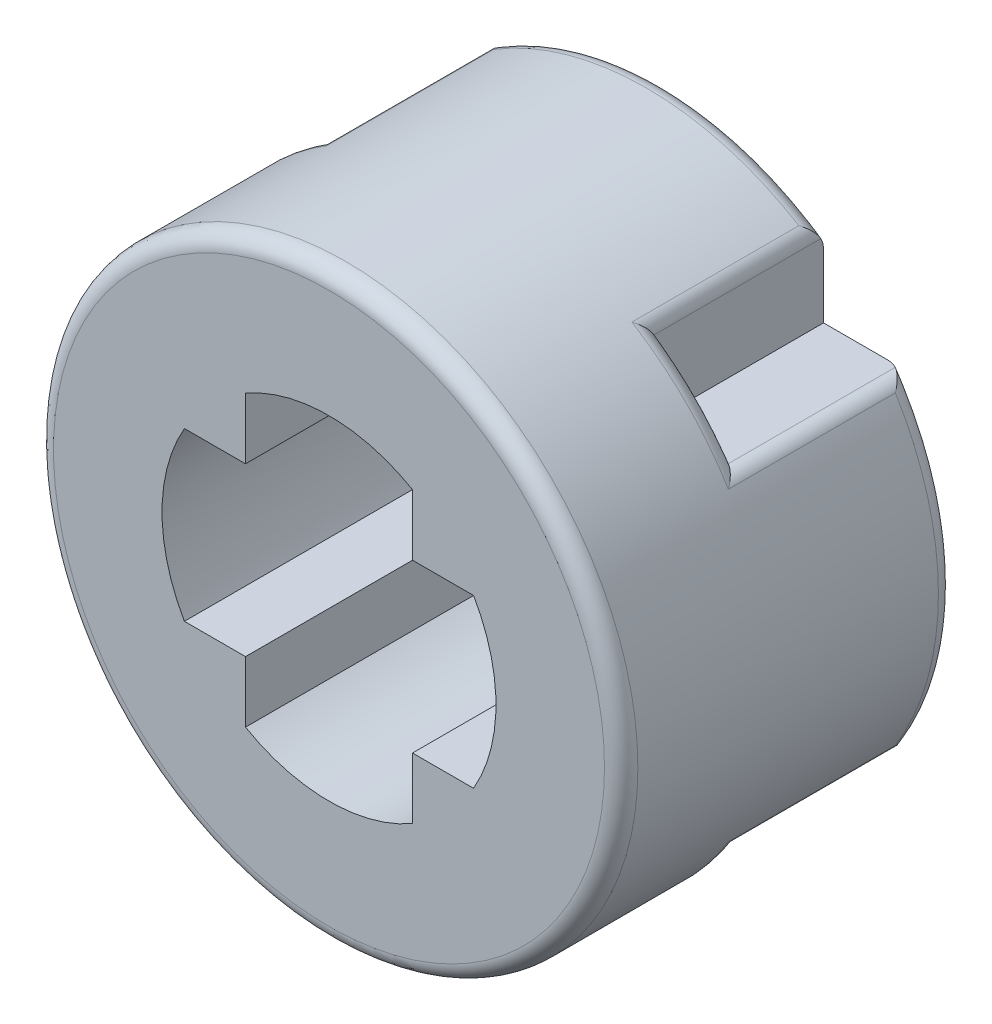
SolidWorks part; units mm, degrees
material "PBT General Purpose"
ref_plane "Front Plane" through (0, 0, 0) normal (0, 0, 1) x (1, 0, 0)
ref_plane "Top Plane" through (0, 0, 0) normal (0, 1, 0) x (1, 0, 0)
ref_plane "Right Plane" through (0, 0, 0) normal (1, 0, 0) x (0, 0, -1)
sketch "Sketch1" plane through (0, 0, 0) normal (0, 0, 1) x (1, 0, 0)
  line L0 (1, -1) -> (1.7321, -1)
  line L2 (-1, -1.7321) -> (-1, -1)
  line L4 (1, -1.7321) -> (1, -1)
  line L7 (-1.7321, -1) -> (-1, -1)
  line L9 (-1.7321, 1) -> (-1, 1)
  line L13 (1, 1) -> (1, 1.7321)
  line L14 (1, 1) -> (1.7321, 1)
  line L15 (-1, 1) -> (-1, 1.7321)
  circle A0 centre (0, 0) radius 3.5
  arc A1 (1, 1.7321) -> (-1, 1.7321) centre (0, 0) ccw
  arc A2 (1.7321, -1) -> (1.7321, 1) centre (0, 0) ccw
  arc A3 (-1, -1.7321) -> (1, -1.7321) centre (0, 0) ccw
  arc A4 (-1.7321, 1) -> (-1.7321, -1) centre (0, 0) ccw
  dimension "D1" = 7
  dimension "D5" = 1
  dimension "D2" = 2
  dimension "D3" = 1
  dimension "D4" = 1
  dimension "D6" = 1
extrude "Boss-Extrude1" add sketch "Sketch1" along normal blind 4
sketch "Sketch2" plane through (0, 0, 0) normal (0, 0, -1) x (-1, 0, 0)
  line L1 (-2.9238, 1.9238) -> (-1.9238, 1.9238)
  line L2 (-2.9238, 1.9238) -> (-2.9238, 2.9238)
  line L3 (-2.9238, 2.9238) -> (-1.9238, 2.9238)
  line L4 (-1.9238, 1.9238) -> (-1.9238, 2.9238)
  line L5 (-2.9238, -1.9238) -> (-1.9238, -1.9238)
  line L6 (-2.9238, -1.9238) -> (-2.9238, -2.9238)
  line L7 (-2.9238, -2.9238) -> (-1.9238, -2.9238)
  line L8 (-1.9238, -1.9238) -> (-1.9238, -2.9238)
  line L9 (1.9238, -2.9238) -> (2.9238, -2.9238)
  line L10 (1.9238, -2.9238) -> (1.9238, -1.9238)
  line L11 (1.9238, -1.9238) -> (2.9238, -1.9238)
  line L12 (2.9238, -2.9238) -> (2.9238, -1.9238)
  line L13 (2.9238, 1.9238) -> (1.9238, 1.9238)
  line L14 (2.9238, 1.9238) -> (2.9238, 2.9238)
  line L15 (2.9238, 2.9238) -> (1.9238, 2.9238)
  line L16 (1.9238, 1.9238) -> (1.9238, 2.9238)
  circle A0 centre (0, 0) radius 3.5 construction
  dimension "D1" = 1
  dimension "D2" = 1
extrude "Cut-Extrude1" cut sketch "Sketch2" against normal blind 2
fillet "Fillet1" radius 0.2 17 edges at (3.5, 0, 4) (-1.9238, 2.9238, 1) (0, 3.5, 0) (1.9238, 2.9238, 1) (2.4749, 2.4749, 2) (2.9238, 1.9238, 1) (3.5, 0, 0) (2.9238, -1.9238, 1) (2.4749, -2.4749, 2) (1.9238, -2.9238, 1) (0, -3.5, 0) (-1.9238, -2.9238, 1) (-2.4749, -2.4749, 2) (-2.9238, -1.9238, 1) (-3.5, 0, 0) (-2.9238, 1.9238, 1) (-2.4749, 2.4749, 2)
